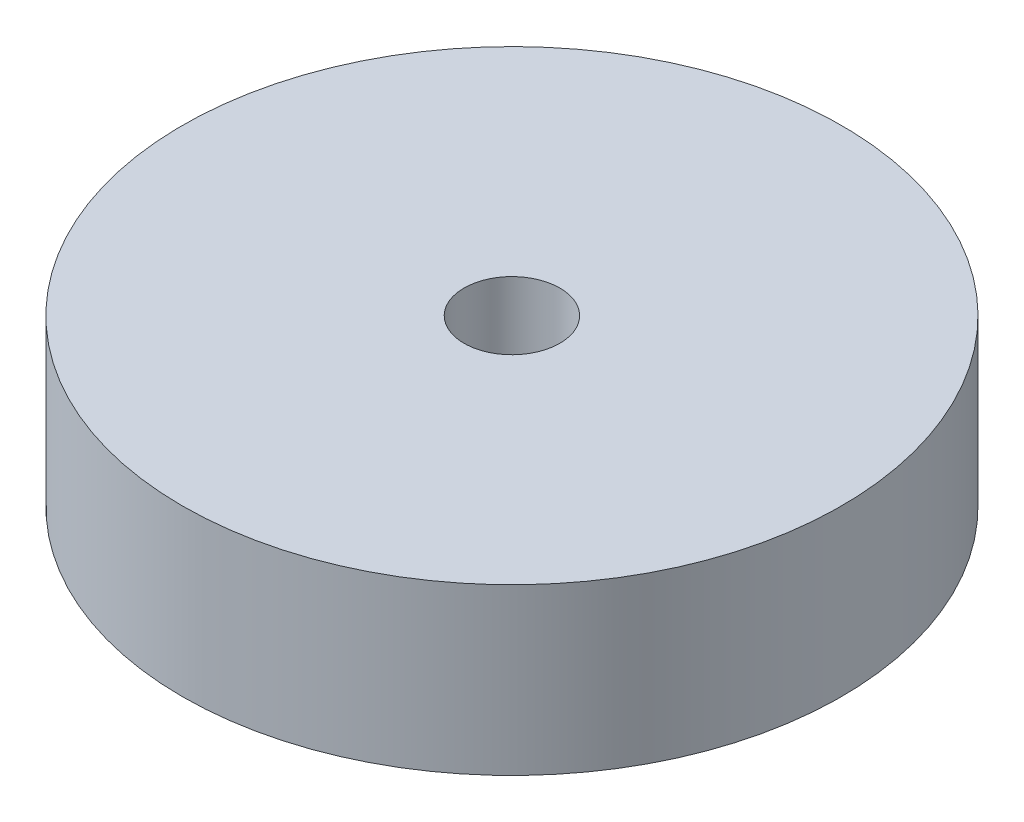
SolidWorks part; units mm, degrees
ref_plane "Front Plane" through (0, 0, 0) normal (0, 0, 1) x (1, 0, 0)
ref_plane "Top Plane" through (0, 0, 0) normal (0, 1, 0) x (1, 0, 0)
ref_plane "Right Plane" through (0, 0, 0) normal (1, 0, 0) x (0, 0, -1)
sketch "Sketch1" plane through (0, 0, 0) normal (0, 1, 0) x (1, 0, 0)
  circle A0 centre (0, 0) radius 19.95
extrude "Boss-Extrude1" add sketch "Sketch1" along normal blind 10
sketch "Sketch2" plane through (0, 0, 0) normal (0, -1, 0) x (-1, 0, 0)
  circle A0 centre (0, 0) radius 5.25
extrude "Cut-Extrude1" cut sketch "Sketch2" against normal blind 5
sketch "Sketch3" plane through (0, 5, 0) normal (0, -1, 0) x (-1, 0, 0)
  circle A0 centre (0, 0) radius 2.9
extrude "Cut-Extrude2" cut sketch "Sketch3" against normal blind 5
